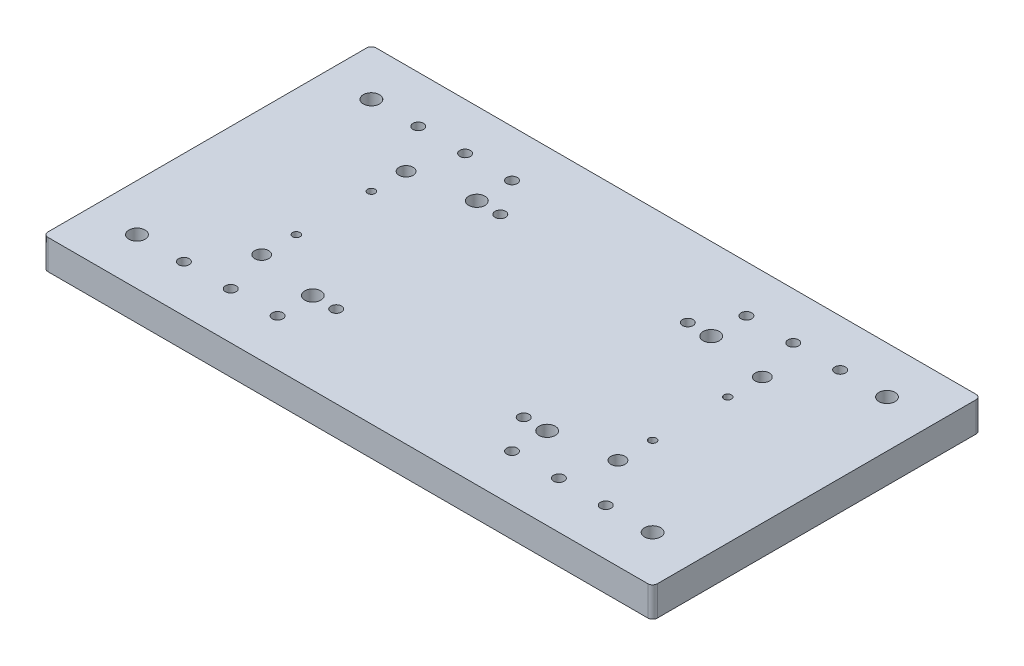
SolidWorks part; units mm, degrees
material "6061 Alloy"
ref_plane "Front Plane" through (0, 0, 0) normal (0, 0, 1) x (1, 0, 0)
ref_plane "Top Plane" through (0, 0, 0) normal (0, 1, 0) x (1, 0, 0)
ref_plane "Right Plane" through (0, 0, 0) normal (1, 0, 0) x (0, 0, -1)
sketch "Sketch1" plane through (0, 0, 0) normal (0, 1, 0) x (1, 0, 0)
  line L0 (10, -10) -> (20, -10) construction
  line L1 (0, 0) -> (130, 0)
  line L2 (0, 0) -> (0, -70)
  line L3 (0, -70) -> (130, -70)
  line L4 (130, 0) -> (130, -70)
  line L5 (20, -10) -> (30, -10) construction
  line L6 (30, -10) -> (40, -10) construction
  line L7 (65, 0) -> (65, -70) construction
  line L8 (130, -35) -> (0, -35) construction
  line L9 (0, 0) -> (0, -70)
  line L10 (15, -5) -> (115, -5) construction
  line L11 (15, -5) -> (15, -65) construction
  line L12 (15, -65) -> (115, -65) construction
  line L13 (115, -5) -> (115, -65) construction
  line L14 (130, 0) -> (130, -70)
  circle A0 centre (10, -10) radius 1.725
  circle A1 centre (20, -10) radius 1.13
  circle A2 centre (30, -10) radius 1.13
  circle A3 centre (40, -10) radius 1.13
  circle A4 centre (45, -17.5) radius 1.13
  circle A5 centre (40, -17.5) radius 1.725
  circle A6 centre (27, -27) radius 0.8
  circle A7 centre (27, -19.6) radius 1.5
  circle A8 centre (27, -43) radius 0.8
  circle A9 centre (27, -50.4) radius 1.5
  circle A10 centre (45, -52.5) radius 1.13
  circle A11 centre (40, -52.5) radius 1.725
  circle A12 centre (40, -60) radius 1.13
  circle A13 centre (30, -60) radius 1.13
  circle A14 centre (20, -60) radius 1.13
  circle A15 centre (10, -60) radius 1.725
  circle A16 centre (120, -60) radius 1.725
  circle A17 centre (110, -60) radius 1.13
  circle A18 centre (100, -60) radius 1.13
  circle A19 centre (90, -60) radius 1.13
  circle A20 centre (85, -52.5) radius 1.13
  circle A21 centre (90, -52.5) radius 1.725
  circle A22 centre (103, -43) radius 0.8
  circle A23 centre (103, -50.4) radius 1.5
  circle A24 centre (103, -19.6) radius 1.5
  circle A25 centre (103, -27) radius 0.8
  circle A26 centre (85, -17.5) radius 1.13
  circle A27 centre (90, -17.5) radius 1.725
  circle A28 centre (90, -10) radius 1.13
  circle A29 centre (100, -10) radius 1.13
  circle A30 centre (110, -10) radius 1.13
  circle A31 centre (120, -10) radius 1.725
  point P23 (65, -5)
  point P24 (115, -35)
  point P27 (65, -35)
  point P32 (0, 0)
  dimension "D3" = 2.26
  dimension "D6" = 3.45
  dimension "D13" = 1.6
  dimension "D18" = 3
  dimension "D1" = 130
  dimension "D2" = 70
  dimension "D4" = 10
  dimension "D5" = 10
  dimension "D7" = 10
  dimension "D8" = 25
  dimension "D9" = 7.5
  dimension "D10" = 100
  dimension "D11" = 60
  dimension "D14" = 20
  dimension "D15" = 17.5
  dimension "D12" = 25
  dimension "D16" = 38
  dimension "D17" = 8
  dimension "D19" = 15.4
extrude "Boss-Extrude1" add sketch "Sketch1" along normal blind 6.35 contours L4 L1 L2 L3 A30 A28 A26 A24 A23 A22 A21 A20 A19 A18 A17 A16 A14 A12 A10 A8 A7 A6 A5 A4 A3 A2 A1
hole_wizard "#4-40 Tapped Hole1" positions "3DSketch1" profile "Sketch2" tap size "#4-40" standard "ANSI Inch" end condition through all
sketch3d "3DSketch1"
  line L0 (40, 6.35, 10) -> (40, 0, 10) construction
  line L1 (30, 6.35, 10) -> (30, 0, 10) construction
  line L2 (110, 6.35, 60) -> (110, 0, 60) construction
  line L3 (100, 6.35, 60) -> (100, 0, 60) construction
  line L4 (90, 6.35, 60) -> (90, 0, 60) construction
  line L5 (40, 6.35, 60) -> (40, 0, 60) construction
  line L6 (30, 6.35, 60) -> (30, 0, 60) construction
  line L7 (20, 6.35, 60) -> (20, 0, 60) construction
  line L8 (110, 6.35, 10) -> (110, 0, 10) construction
  line L9 (100, 6.35, 10) -> (100, 0, 10) construction
  line L10 (45, 6.35, 17.5) -> (45, 0, 17.5) construction
  line L11 (85, 6.35, 17.5) -> (85, 0, 17.5) construction
  line L12 (85, 6.35, 52.5) -> (85, 0, 52.5) construction
  line L13 (45, 6.35, 52.5) -> (45, 0, 52.5) construction
  circle A0 centre (90, 6.35, 10) radius 1.13 construction
  circle A1 centre (20, 6.35, 10) radius 1.13 construction
  point P0 (40, 6.35, 10)
  point P4 (30, 6.35, 10)
  point P8 (20, 6.35, 10)
  point P10 (90, 6.35, 10)
  point P16 (110, 6.35, 60)
  point P20 (100, 6.35, 60)
  point P24 (90, 6.35, 60)
  point P28 (40, 6.35, 60)
  point P32 (30, 6.35, 60)
  point P36 (20, 6.35, 60)
  point P40 (110, 6.35, 10)
  point P44 (100, 6.35, 10)
  point P58 (90, 5.22, 10)
  point P62 (20, 7.48, 10)
  point P63 (45, 6.35, 17.5)
  point P67 (85, 6.35, 17.5)
  point P71 (85, 6.35, 52.5)
  point P75 (45, 6.35, 52.5)
sketch "Sketch2" plane through (40, 6.35, 10) normal (1, 0, 0) x (0, 0, 1)
  line L0 (0, 0) -> (0, 6.35)
  line L1 (0, 6.35) -> (1.1303, 6.35)
  line L2 (1.1303, 6.35) -> (1.1303, 0)
  line L5 (1.1303, 0) -> (0, 0)
  line L11 (0, -6.35) -> (0, 107.95) construction
  dimension "Thru Tap Drill Dia." = 2.2606
  dimension "Thru Tap Drill Depth" = 6.35
cosmetic thread "Hole Thread1" parameters "D2"=2.8448
cosmetic thread "Hole Thread2" parameters "D2"=2.8448
cosmetic thread "Hole Thread3" parameters "D2"=2.8448
cosmetic thread "Hole Thread4" parameters "D2"=2.8448
cosmetic thread "Hole Thread5" parameters "D2"=2.8448
cosmetic thread "Hole Thread6" parameters "D2"=2.8448
cosmetic thread "Hole Thread7" parameters "D2"=2.8448
cosmetic thread "Hole Thread8" parameters "D2"=2.8448
cosmetic thread "Hole Thread9" parameters "D2"=2.8448
cosmetic thread "Hole Thread10" parameters "D2"=2.8448
cosmetic thread "Hole Thread11" parameters "D2"=2.8448
cosmetic thread "Hole Thread12" parameters "D2"=2.8448
cosmetic thread "Hole Thread13" parameters "D2"=2.8448
cosmetic thread "Hole Thread14" parameters "D2"=2.8448
cosmetic thread "Hole Thread15" parameters "D2"=2.8448
cosmetic thread "Hole Thread16" parameters "D2"=2.8448
fillet "Fillet1" radius 1 4 edges at (130, 3.175, 0) (130, 3.175, 70) (0, 3.175, 70) (0, 3.175, 0)
equation "\"D5@Sketch1\"=\"D4@Sketch1\""
